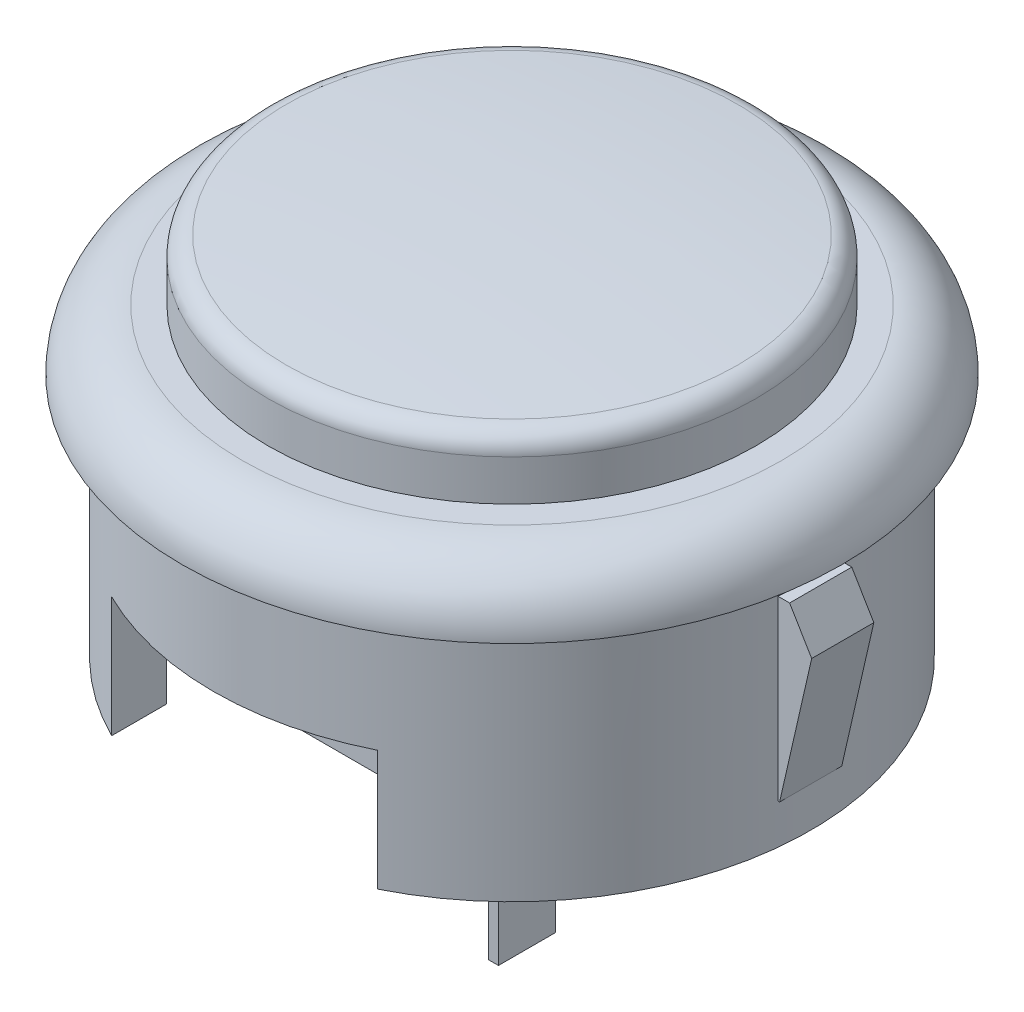
SolidWorks part; units mm, degrees
ref_plane "Front Plane" through (0, 0, 0) normal (0, 0, 1) x (1, 0, 0)
ref_plane "Top Plane" through (0, 0, 0) normal (0, 1, 0) x (1, 0, 0)
ref_plane "Right Plane" through (0, 0, 0) normal (1, 0, 0) x (0, 0, -1)
sketch "Sketch1" plane through (0, 0, 0) normal (0, 0, 1) x (1, 0, 0)
  line L0 (0, 7.971) -> (0, -12.25) construction
  line L1 (16.45, 0) -> (14.9, 0)
  line L2 (14.9, 0) -> (14.9, -12.25)
  line L3 (14.9, -12.25) -> (12.5, -12.25)
  line L4 (12.5, -12.25) -> (12.5, -6.25)
  line L5 (12.5, -6.25) -> (0, -6.25)
  line L6 (0, -6.25) -> (0, 6.55)
  line L7 (12.175, 5.0406) -> (12.175, 3)
  line L8 (12.175, 3) -> (13.45, 3)
  line L9 (0, 6.55) -> (8.8028, 6.55) construction
  arc A0 (13.45, 3) -> (16.45, 0) centre (13.45, 0) cw
  arc A1 (0, 6.55) -> (11.266, 6.0364) centre (0, -117.2755) cw
  arc A2 (12.175, 5.0406) -> (11.266, 6.0364) centre (11.175, 5.0406) ccw
  point P14 (0, -17.3138)
  point P17 (0, -17.3138)
  point P18 (10.7275, 3.376)
  point P19 (0, -12.25)
  point P20 (0, 6.92)
  point P21 (10.8649, 4.244)
  point P22 (0, 6.1016)
  point P23 (10.5922, 4.7212)
  point P24 (8.8028, 6.55)
  point P25 (0, 7.971)
  point P28 (12.175, 5.95)
  dimension "D1" = 12.25
  dimension "D9" = 1
  dimension "D2" = 25
  dimension "D3" = 29.8
  dimension "D4" = 6
  dimension "D5" = 32.9
  dimension "D6" = 18.8
  dimension "D7" = 24.35
  dimension "D8" = 0.6
  dimension "D10" = 3
revolve "Revolve1" add sketch "Sketch1" angle 360 about L0
sketch "Sketch2" plane through (0, 0, 0) normal (0, 0, 1) x (1, 0, 0)
  line L0 (0, 0) -> (0, -15.2837) construction
  line L1 (-14.9, -12.25) -> (14.9, -12.25) construction
  line L2 (6.625, -6.25) -> (-6.625, -6.25)
  line L3 (6.625, -6.25) -> (6.625, -12.25)
  line L4 (6.625, -12.25) -> (-6.625, -12.25)
  line L5 (-6.625, -6.25) -> (-6.625, -12.25)
  line L6 (6.625, -6.25) -> (-6.625, -12.25) construction
  line L7 (6.625, -12.25) -> (-6.625, -6.25) construction
  point P3 (0, -9.25)
  dimension "D1" = 13.25
  dimension "D2" = 6
extrude "Cut-Extrude1" cut sketch "Sketch2" against normal through all both and the other way through all
sketch "Sketch3" plane through (0, 0, 0) normal (0, 0, 1) x (1, 0, 0)
  line L0 (0, 8.7681) -> (0, -10.774) construction
  line L1 (14.9, -10.25) -> (16.5, -3.25)
  line L2 (14.9, -12.25) -> (14.9, 0) construction
  line L3 (16.5, -3.25) -> (15.4, -1.4)
  line L4 (15.4, -1.4) -> (13.9, -1.4)
  line L5 (14.9, -10.25) -> (13.9, -10.25)
  line L6 (13.9, -10.25) -> (13.9, -1.4)
  line L7 (6.625, -12.25) -> (14.9, -12.25) construction
  line L9 (-16.45, 0) -> (16.45, 0) construction
  point P11 (15.1697, -1.25)
  point P13 (15.2982, -1.25)
  point P14 (16.5, -3.25)
  point P15 (15.0154, -1.25)
  point P16 (14.9, -10.25)
  point P17 (14.4241, -10.25)
  point P18 (15.4396, -1.25)
  dimension "D1" = 33
  dimension "D2" = 9
  dimension "D3" = 1.4
  dimension "D4" = 2
  dimension "D5" = 0.5
  dimension "D6" = 1
extrude "Boss-Extrude1" add sketch "Sketch3" along normal mid plane 3.1
mirror "Mirror1" about plane through (0, 0, 0) normal (1, 0, 0) of "Boss-Extrude1"
sketch "Sketch4" plane through (0, -6.25, 0) normal (0, -1, 0) x (1, 0, 0)
  line L1 (-6, -6.375) -> (6, -6.375)
  line L2 (-6, -6.375) -> (-6, 6.375)
  line L3 (-6, 6.375) -> (6, 6.375)
  line L4 (6, -6.375) -> (6, 6.375)
  line L5 (-6, -6.375) -> (6, 6.375) construction
  line L6 (-6, 6.375) -> (6, -6.375) construction
  point P0 (0, 0)
  dimension "D1" = 12.75
  dimension "D2" = 12
extrude "Boss-Extrude2" add sketch "Sketch4" along normal blind 8
sketch "Sketch5" plane through (0, -14.25, 0) normal (0, -1, 0) x (1, 0, 0)
  line L0 (6, -6.375) -> (6, 6.375) construction
  line L1 (2.2, 3.375) -> (2.7, 3.375)
  line L2 (2.2, 3.375) -> (2.2, 0.525)
  line L3 (2.2, 0.525) -> (2.7, 0.525)
  line L4 (2.7, 3.375) -> (2.7, 0.525)
  line L5 (-2.7, -0.525) -> (-2.2, -0.525)
  line L6 (-2.7, -0.525) -> (-2.7, -3.375)
  line L7 (-2.7, -3.375) -> (-2.2, -3.375)
  line L8 (-2.2, -0.525) -> (-2.2, -3.375)
  line L9 (-6, 6.375) -> (-6, -6.375) construction
  line L10 (-6, -6.375) -> (6, -6.375) construction
  line L11 (6, 6.375) -> (-6, 6.375) construction
  point P16 (-1.904, -3.375)
  dimension "D1" = 3.3
  dimension "D2" = 3.3
  dimension "D3" = 2.85
  dimension "D4" = 3
  dimension "D5" = 3
  dimension "D6" = 0.5
extrude "Boss-Extrude3" add sketch "Sketch5" along normal blind 8.25
